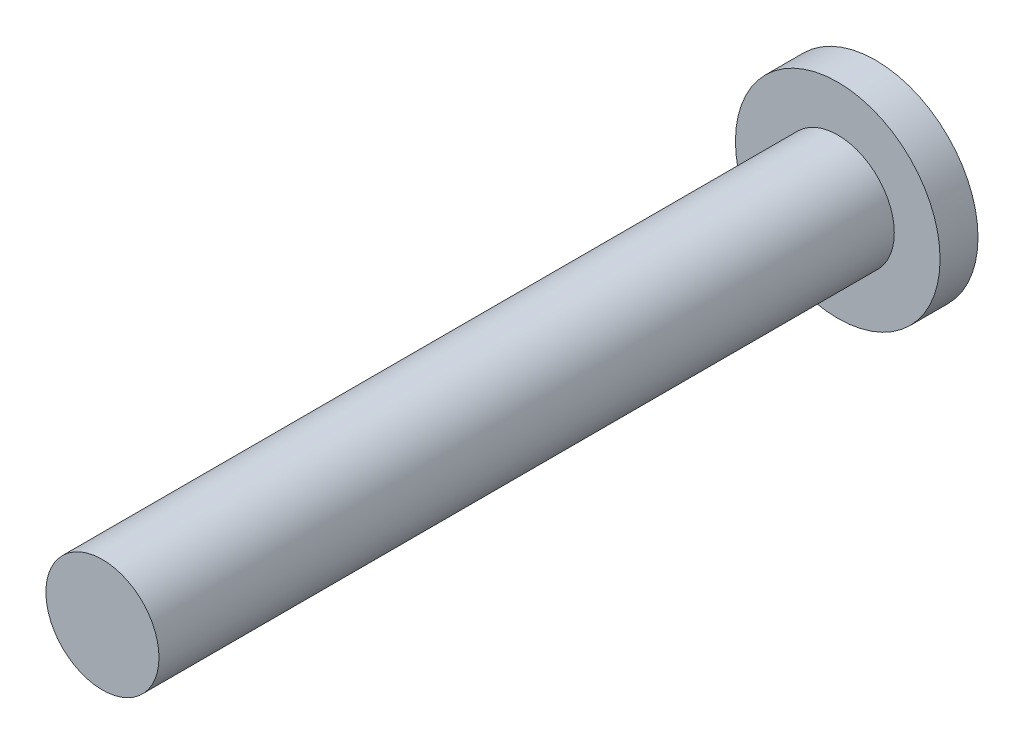
SolidWorks part; units mm, degrees
ref_plane "Front Plane" through (0, 0, 0) normal (0, 0, 1) x (1, 0, 0)
ref_plane "Top Plane" through (0, 0, 0) normal (0, 1, 0) x (1, 0, 0)
ref_plane "Right Plane" through (0, 0, 0) normal (1, 0, 0) x (0, 0, -1)
sketch "Sketch1" plane through (0, 0, 0) normal (0, 0, 1) x (1, 0, 0)
  circle A0 centre (0, 0) radius 4.425
  dimension "D1" = 8.85
extrude "Boss-Extrude1" add sketch "Sketch1" along normal blind 1.64
sketch "Sketch2" plane through (0, 0, 1.64) normal (0, 0, 1) x (1, 0, 0)
  circle A0 centre (0, 0) radius 2.445
  dimension "D1" = 4.89
extrude "Boss-Extrude2" add sketch "Sketch2" along normal blind 31.8
